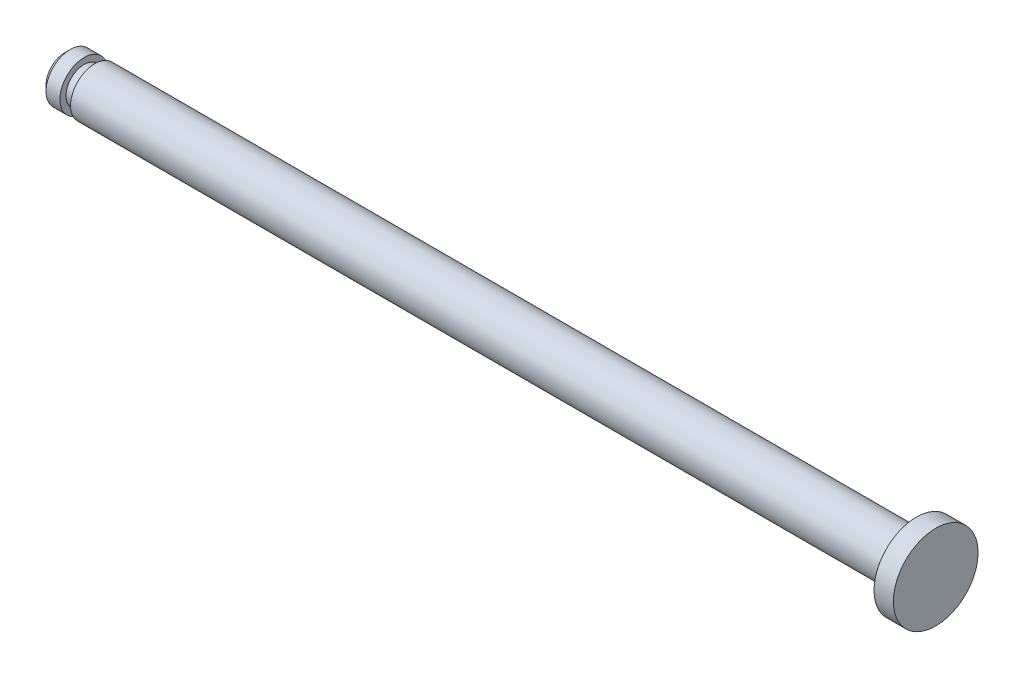
SolidWorks part; units mm, degrees
material "Acier inoxydable chromé"
ref_plane "Plan de face" through (0, 0, 0) normal (0, 0, 1) x (1, 0, 0)
ref_plane "Plan de dessus" through (0, 0, 0) normal (0, 1, 0) x (1, 0, 0)
ref_plane "Plan de droite" through (0, 0, 0) normal (1, 0, 0) x (0, 0, -1)
sketch "Esquisse3" plane through (0, 0, 0) normal (0, 0, 1) x (1, 0, 0)
  line L0 (-40.2815, 0) -> (3.463, 0) construction
  line L1 (-0.8, 1) -> (-0.8, 1.75)
  line L2 (-36, 0) -> (0, 0)
  line L3 (-36, 0) -> (-36, 0.7753)
  line L4 (-35.7753, 1) -> (-35.2, 1)
  line L5 (-35.2, 1) -> (-35.2, 0.75)
  line L6 (-0.8, 1.75) -> (0, 1.75)
  line L7 (0, 1.75) -> (0, 0)
  line L8 (-35.2, 0.75) -> (-34.76, 0.75)
  line L9 (-34.76, 0.75) -> (-34.76, 1)
  line L10 (-34.76, 1) -> (-0.8, 1)
  line L11 (-35.7753, 1) -> (-36, 0.7753)
  dimension "D1" = 36
  dimension "D2" = 1
  dimension "D3" = 0.8
  dimension "D4" = 1.75
  dimension "D5" = 0.44
  dimension "D6" = 0.75
revolve "Révolution1" add sketch "Esquisse3" angle 360 about L0
